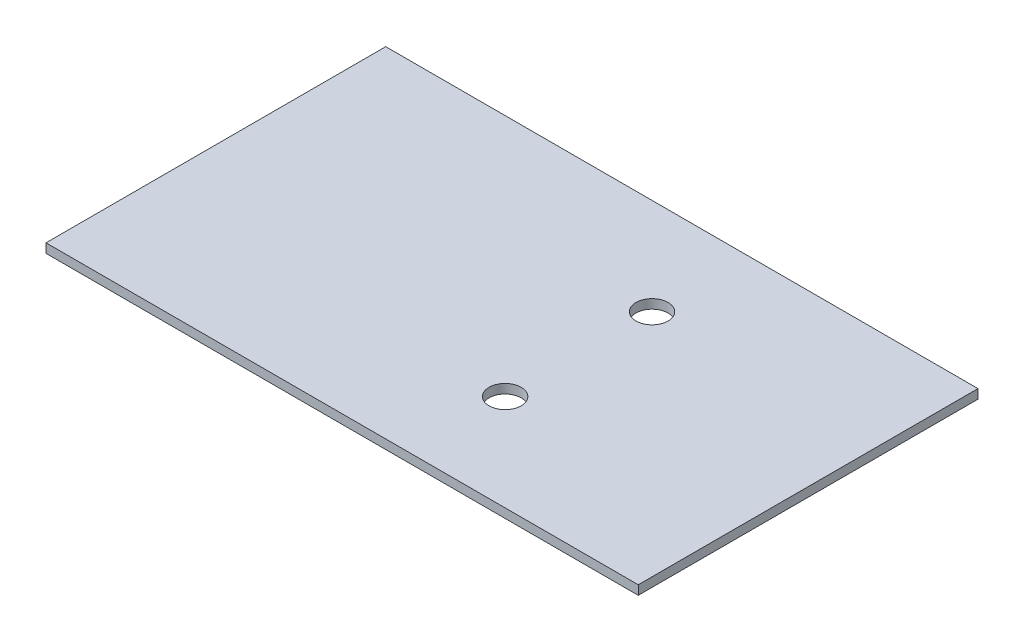
SolidWorks part; units mm, degrees
material "Acrylic (Medium-high impact)"
ref_plane "Front Plane" through (0, 0, 0) normal (0, 0, 1) x (1, 0, 0)
ref_plane "Top Plane" through (0, 0, 0) normal (0, 1, 0) x (1, 0, 0)
ref_plane "Right Plane" through (0, 0, 0) normal (1, 0, 0) x (0, 0, -1)
sketch "Sketch1" plane through (0, 0, 0) normal (0, 1, 0) x (1, 0, 0)
  line L1 (0, 0) -> (129, 0)
  line L2 (0, 0) -> (0, -74)
  line L3 (0, -74) -> (129, -74)
  line L4 (129, 0) -> (129, -74)
  dimension "D1" = 129
  dimension "D2" = 74
extrude "Boss-Extrude1" add sketch "Sketch1" along normal blind 2
sketch "Sketch2" plane through (0, 0, 0) normal (0, -1, 0) x (1, 0, 0)
  line L0 (129, 74) -> (129, 0) construction
  line L1 (0, 74) -> (129, 74) construction
  line L2 (129, 0) -> (0, 0) construction
  circle A0 centre (79, 21) radius 3.5
  circle A1 centre (79, 53) radius 3.5
  dimension "D1" = 7
  dimension "D2" = 7
  dimension "D3" = 50
  dimension "D4" = 21
  dimension "D5" = 50
  dimension "D6" = 21
extrude "Cut-Extrude1" cut sketch "Sketch2" against normal through all
